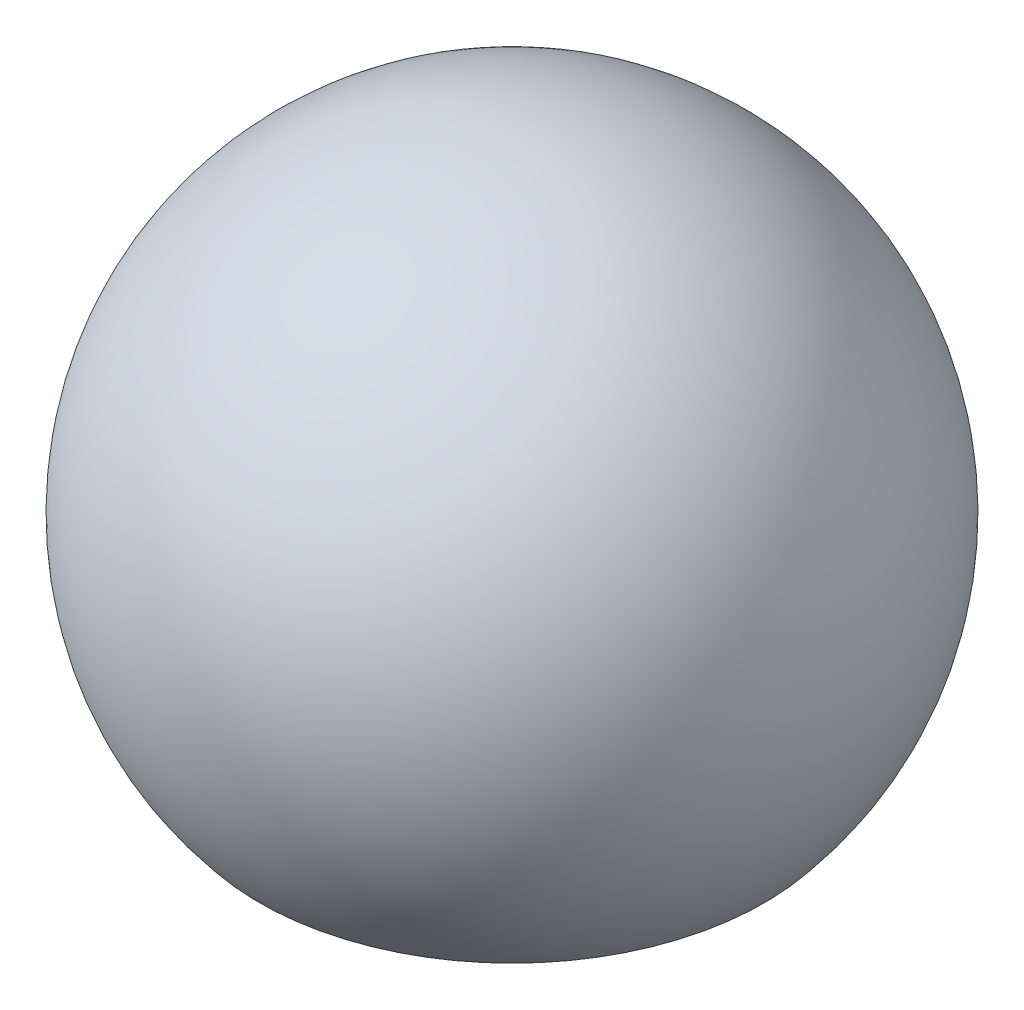
SolidWorks part; units mm, degrees
ref_plane "Front Plane" through (0, 0, 0) normal (0, 0, 1) x (1, 0, 0)
ref_plane "Top Plane" through (0, 0, 0) normal (0, 1, 0) x (1, 0, 0)
ref_plane "Right Plane" through (0, 0, 0) normal (1, 0, 0) x (0, 0, -1)
sketch "Sketch2" plane through (0, 0, 0) normal (0, 0, 1) x (1, 0, 0)
  line L0 (0, -528.4602) -> (0, 2100) construction
  line L5 (459.6267, 114.3274) -> (1225.6711, -528.4602)
  line L6 (-459.6267, 114.3274) -> (-1225.6711, -528.4602)
  arc A0 (-459.6267, 114.3274) -> (459.6267, 114.3274) centre (0, 500) cw
  arc A1 (-1225.6711, -528.4602) -> (1225.6711, -528.4602) centre (0, 500) cw
  dimension "D1" = 260
  dimension "D5" = 1000
revolve "Reachable workspace" add sketch "Sketch2" angle 360 about L0
sketch "Sketch3" plane through (0, 0, 0) normal (1, 0, 0) x (0, 0, -1)
  line L0 (1519.8684, 0) -> (-1519.8684, 0) construction
  arc A0 (1225.6711, -528.4602) -> (-1225.6711, -528.4602) centre (0, 500) ccw construction
sketch "Sketch4" plane through (0, 0, 0) normal (0, 0, 1) x (1, 0, 0)
  line L0 (1519.8684, 0) -> (-1519.8684, 0) construction
  arc A0 (1225.6711, -528.4602) -> (-1225.6711, -528.4602) centre (0, 500) ccw construction
  arc A1 (1225.6711, -528.4602) -> (-1225.6711, -528.4602) centre (0, 500) ccw construction
